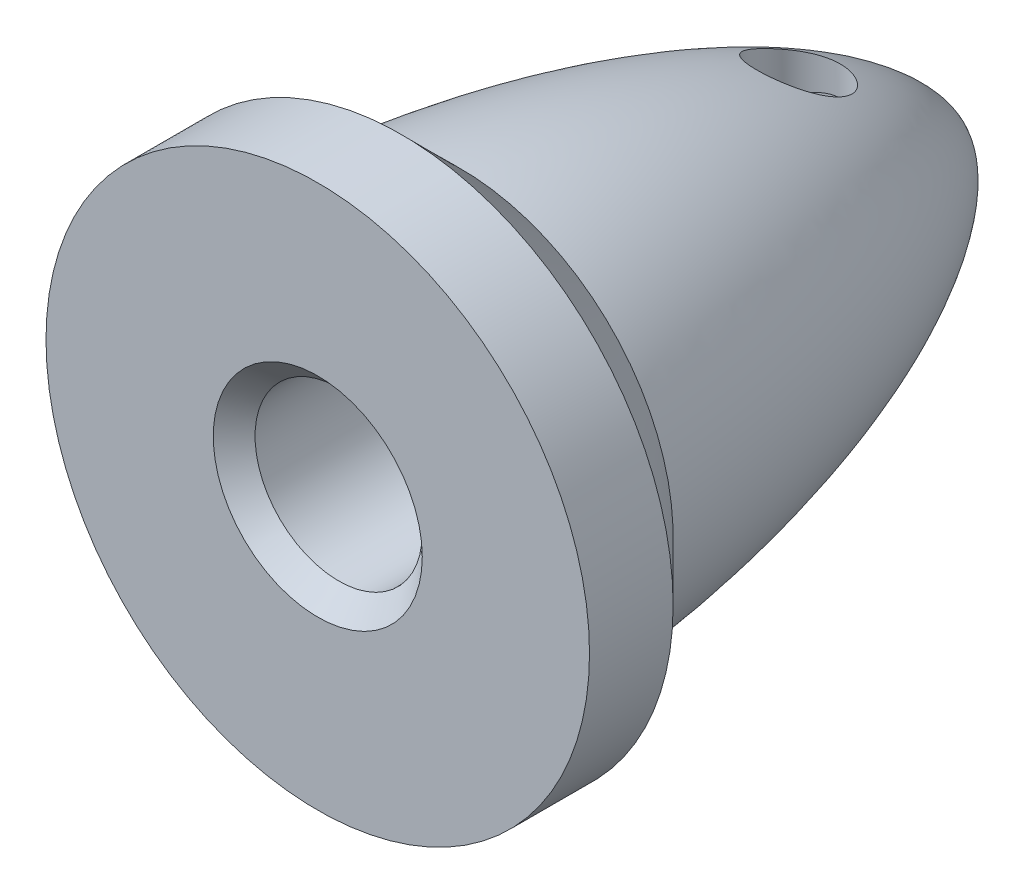
SolidWorks part; units mm, degrees
material "TIMETAL 35A CP Titanio (ASTM Grado 1) 99.1 Ti"
ref_plane "Alzado" through (0, 0, 0) normal (0, 0, 1) x (1, 0, 0)
ref_plane "Planta" through (0, 0, 0) normal (0, 1, 0) x (1, 0, 0)
ref_plane "Vista lateral" through (0, 0, 0) normal (1, 0, 0) x (0, 0, -1)
sketch "Croquis1" plane through (0, 0, 0) normal (0, 1, 0) x (1, 0, 0)
  line L0 (0, 14.3448) -> (0, -7.6) construction
  line L1 (0, -7.6) -> (-6.5, -7.6)
  line L2 (-6.5, -7.6) -> (-6.5, -5.6)
  line L3 (-6.5, -5.6) -> (-5.0858, -4.1858)
  line L4 (0, -7.6) -> (0, 7.6)
  spline S0 degree 3 poles (-5.0858, -4.1858) (-4.4574, 2.6863) (-1.9717, 7.4114) (0, 7.6) knots 0 0 0 0 1 1 1 1
  point P3 (0, 0)
  point P8 (0, 0)
  dimension "D1" = 2
  dimension "D2" = 2
  dimension "D3" = 6.5
  dimension "D4" = 15.2
  dimension "D5" = 45
revolve "Revolución1" add sketch "Croquis1" angle 360 about L0
sketch "Croquis2" plane through (0, 0, 0) normal (0, 1, 0) x (1, 0, 0)
  line L0 (-6.5, -7.6) -> (6.5, -7.6) construction
  line L1 (0, 7.6) -> (0, 0) construction
  circle A0 centre (0, 3.9) radius 0.9976
  point P5 (0, 3.8)
  point P9 (1.4446, 3.9)
  point P10 (0, 0)
  dimension "D2" = 1.9951
  dimension "D1" = 11.5
extrude "Cortar-Extruir1" cut sketch "Croquis2" against normal mid plane 10
sketch "Croquis4" plane through (0, 0, 7.6) normal (0, 0, 1) x (1, 0, 0)
  circle A0 centre (0, 0) radius 2
  dimension "D1" = 4
extrude "Cortar-Extruir2" cut sketch "Croquis4" against normal blind 13.5
chamfer "Chaflán1" distance 0.5 angle 45 1 edges at (2, 0, 7.6)
